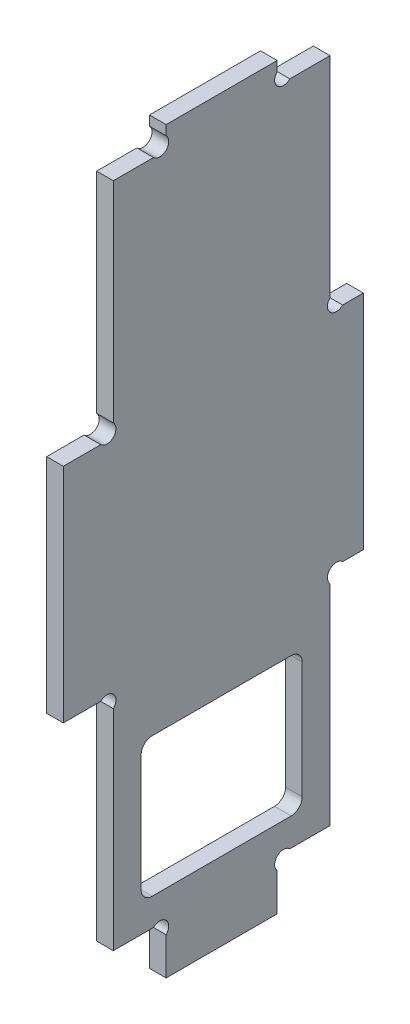
SolidWorks part; units mm, degrees
ref_plane "Plan de face" through (0, 0, 0) normal (0, 0, 1) x (1, 0, 0)
ref_plane "Plan de dessus" through (0, 0, 0) normal (0, 1, 0) x (1, 0, 0)
ref_plane "Plan de droite" through (0, 0, 0) normal (1, 0, 0) x (0, 0, -1)
sketch "Esquisse1" plane through (0, 0, 0) normal (1, 0, 0) x (0, 0, -1)
  line L13 (18.5, 6.7373) -> (18.5, 0)
  line L15 (16.2373, 9) -> (9, 9)
  line L17 (50.2627, 49) -> (54, 49)
  line L18 (6.7373, 49) -> (0, 49)
  line L19 (38.5, 6.7373) -> (38.5, 0)
  line L20 (50.2627, 89) -> (54, 89)
  line L21 (6.7373, 89) -> (0, 89)
  line L22 (18.5, 0) -> (38.5, 0)
  line L23 (40.7627, 9) -> (48, 9)
  line L24 (48, 9) -> (48, 46.7373)
  line L25 (9, 9) -> (9, 46.7373)
  line L26 (54, 89) -> (54, 49)
  line L27 (0, 49) -> (0, 89)
  line L29 (18.5, 131.2627) -> (18.5, 133)
  line L30 (38.5, 131.2627) -> (38.5, 133)
  line L31 (9, 91.2627) -> (9, 129)
  line L32 (9, 129) -> (16.2373, 129)
  line L33 (18.5, 133) -> (38.5, 133)
  line L34 (40.7627, 129) -> (48, 129)
  line L35 (48, 129) -> (48, 91.2627)
  arc A0 (50.2627, 49) -> (48, 46.7373) centre (49.1314, 47.8686) ccw
  arc A1 (9, 46.7373) -> (6.7373, 49) centre (7.8686, 47.8686) ccw
  arc A2 (18.5, 6.7373) -> (16.2373, 9) centre (17.3686, 7.8686) ccw
  arc A3 (38.5, 6.7373) -> (40.7627, 9) centre (39.6314, 7.8686) cw
  arc A4 (9, 91.2627) -> (6.7373, 89) centre (7.8686, 90.1314) cw
  arc A5 (50.2627, 89) -> (48, 91.2627) centre (49.1314, 90.1314) cw
  arc A6 (16.2373, 129) -> (18.5, 131.2627) centre (17.3686, 130.1314) ccw
  arc A7 (40.7627, 129) -> (38.5, 131.2627) centre (39.6314, 130.1314) cw
  point P1 (12.6186, 9)
  dimension "D14" = 1.1314
  dimension "D15" = 1.1314
  dimension "D17" = 1.1314
  dimension "D23" = 1.1314
  dimension "D10" = 1.6
  dimension "D1" = 6
  dimension "D2" = 9
  dimension "D3" = 9.5
  dimension "D4" = 9.5
  dimension "D5" = 9
  dimension "D6" = 40
  dimension "D7" = 40
  dimension "D8" = 40
  dimension "D9" = 4
  dimension "D11" = 1.1314
  dimension "D12" = 1.1314
  dimension "D13" = 1.1314
  dimension "D16" = 20
  dimension "D18" = 1.1314
  dimension "D19" = 1.1314
  dimension "D20" = 1.1314
  dimension "D21" = 1.1314
  dimension "D22" = 1.1314
  dimension "D24" = 3.7373
  dimension "D25" = 1.7373
  dimension "D26" = 1.1314
  dimension "D27" = 7.2373
  dimension "D28" = 1.1314
  dimension "D29" = 1.7373
  dimension "D30" = 20
  dimension "D31" = 39
  dimension "D32" = 39
extrude "Extrusion1" add sketch "Esquisse1" along normal blind 3
sketch "Esquisse2" plane through (3, 0, 0) normal (1, 0, 0) x (0, 0, -1)
  line L0 (9, 46.7373) -> (9, 9) construction
  line L1 (14, 14) -> (43, 14)
  line L2 (14, 14) -> (14, 39)
  line L3 (14, 39) -> (43, 39)
  line L4 (43, 14) -> (43, 39)
  line L5 (48, 9) -> (48, 46.7373) construction
  line L6 (9, 9) -> (16.2373, 9) construction
  dimension "D1" = 5
  dimension "D2" = 5
  dimension "D3" = 5
  dimension "D4" = 25
extrude "Enlèv. mat.-Extru.1" cut sketch "Esquisse2" against normal through all
fillet "Congé1" radius 2 4 edges at (1.5, 14, -43) (1.5, 14, -14) (1.5, 39, -14) (1.5, 39, -43)
